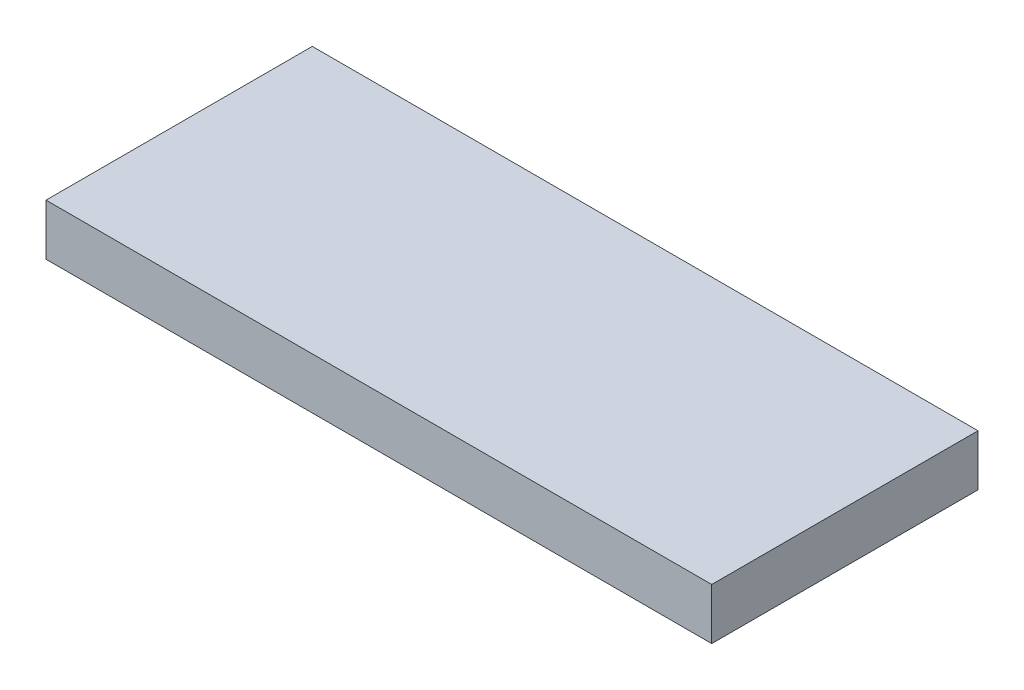
SolidWorks part; units mm, degrees
ref_plane "Front Plane" through (0, 0, 0) normal (0, 0, 1) x (1, 0, 0)
ref_plane "Top Plane" through (0, 0, 0) normal (0, 1, 0) x (1, 0, 0)
ref_plane "Right Plane" through (0, 0, 0) normal (1, 0, 0) x (0, 0, -1)
sketch "Sketch1" plane through (0, 0, 0) normal (0, 1, 0) x (1, 0, 0)
  line L1 (-41.275, -16.51) -> (41.275, -16.51)
  line L2 (-41.275, -16.51) -> (-41.275, 16.51)
  line L3 (-41.275, 16.51) -> (41.275, 16.51)
  line L4 (41.275, -16.51) -> (41.275, 16.51)
  line L5 (-41.275, -16.51) -> (41.275, 16.51) construction
  line L6 (-41.275, 16.51) -> (41.275, -16.51) construction
  point P0 (0, 0)
  dimension "D1" = 33.02
  dimension "D2" = 82.55
extrude "Boss-Extrude1" add sketch "Sketch1" along normal blind 6.35
